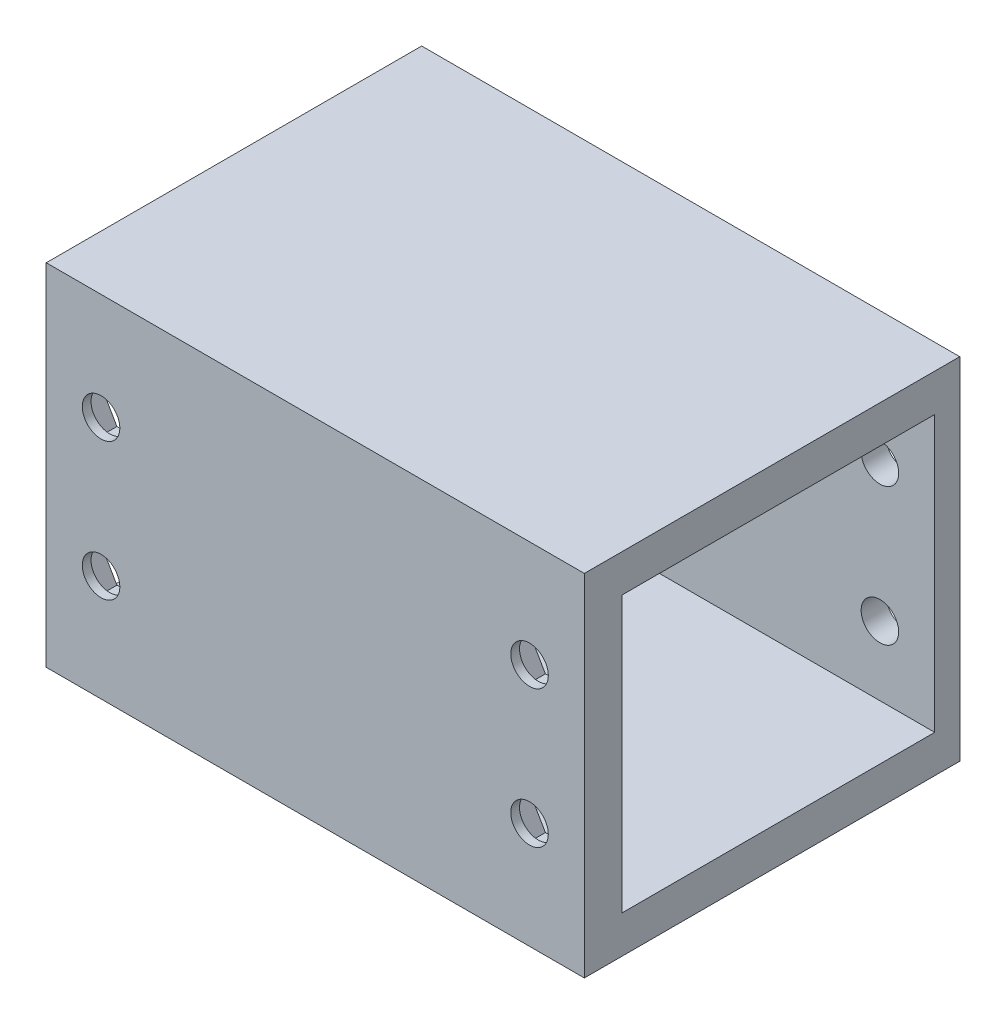
SolidWorks part; units mm, degrees
ref_plane "Front Plane" through (0, 0, 0) normal (0, 0, 1) x (1, 0, 0)
ref_plane "Top Plane" through (0, 0, 0) normal (0, 1, 0) x (1, 0, 0)
ref_plane "Right Plane" through (0, 0, 0) normal (1, 0, 0) x (0, 0, -1)
sketch "Sketch19" plane through (0, 0, 0) normal (1, 0, 0) x (0, 0, -1)
  line L1 (16, 4) -> (-14, 4)
  line L2 (16, 4) -> (16, -24)
  line L3 (16, -24) -> (-14, -24)
  line L4 (-14, 4) -> (-14, -24)
  line L9 (1.5, 1) -> (1.5, -21) construction
  line L10 (-11, -10) -> (14, -10) construction
  line L11 (14, -21) -> (-11, -21)
  line L12 (14, -21) -> (14, 1)
  line L13 (14, 1) -> (-11, 1)
  line L14 (-11, -21) -> (-11, 1)
  line L15 (1.5, 1) -> (1.5, -21) construction
  line L16 (14, -10) -> (-11, -10) construction
  point P4 (1.5, -10)
  point P6 (1.5, -10)
  point P10 (-14, -10)
  dimension "D1" = 30
  dimension "D2" = 3
  dimension "D3" = 3
  dimension "D4" = 2
  dimension "D5" = 3
extrude "Boss-Extrude1" add sketch "Sketch19" against normal blind 43
sketch "Sketch30" plane through (0, 0, 14) normal (0, 0, 1) x (1, 0, 0)
  line L2 (0, -24) -> (0, 4) construction
  line L3 (-43, -24) -> (-43, 4) construction
  circle A0 centre (-38.62, -4.5087) radius 1.5
  circle A1 centre (-4.38, -4.5087) radius 1.5
  circle A2 centre (-4.38, -15.4913) radius 1.5
  circle A3 centre (-38.62, -15.4913) radius 1.5
  point P12 (0, 0)
  point P13 (0, 0)
  point P14 (0, 0)
  point P15 (0, 0)
  dimension "D1" = 3
  dimension "D2" = 3
  dimension "D3" = 3
  dimension "D4" = 3
  dimension "D5" = 4.38
  dimension "D6" = 4.38
  dimension "D7" = 4.38
  dimension "D8" = 4.38
extrude "Cut-Extrude2" cut sketch "Sketch30" against normal through all
sketch "Sketch31" plane through (0, 0, 11) normal (0, 0, -1) x (-1, 0, 0)
  line L1 (42.0841, -4.5087) -> (40.3521, -1.5087)
  line L2 (40.3521, -1.5087) -> (36.8879, -1.5087)
  line L3 (36.8879, -1.5087) -> (35.1559, -4.5087)
  line L4 (35.1559, -4.5087) -> (36.8879, -7.5087)
  line L5 (36.8879, -7.5087) -> (40.3521, -7.5087)
  line L6 (40.3521, -7.5087) -> (42.0841, -4.5087)
  line L7 (7.8441, -4.5087) -> (6.1121, -1.5087)
  line L8 (6.1121, -1.5087) -> (2.6479, -1.5087)
  line L9 (2.6479, -1.5087) -> (0.9159, -4.5087)
  line L10 (0.9159, -4.5087) -> (2.6479, -7.5087)
  line L11 (2.6479, -7.5087) -> (6.1121, -7.5087)
  line L12 (6.1121, -7.5087) -> (7.8441, -4.5087)
  line L13 (7.8441, -15.4913) -> (6.1121, -12.4913)
  line L14 (6.1121, -12.4913) -> (2.6479, -12.4913)
  line L15 (2.6479, -12.4913) -> (0.9159, -15.4913)
  line L16 (0.9159, -15.4913) -> (2.6479, -18.4913)
  line L17 (2.6479, -18.4913) -> (6.1121, -18.4913)
  line L18 (6.1121, -18.4913) -> (7.8441, -15.4913)
  line L19 (42.0841, -15.4913) -> (40.3521, -12.4913)
  line L20 (40.3521, -12.4913) -> (36.8879, -12.4913)
  line L21 (36.8879, -12.4913) -> (35.1559, -15.4913)
  line L22 (35.1559, -15.4913) -> (36.8879, -18.4913)
  line L23 (36.8879, -18.4913) -> (40.3521, -18.4913)
  line L24 (40.3521, -18.4913) -> (42.0841, -15.4913)
  circle A0 centre (38.62, -4.5087) radius 3 construction
  circle A1 centre (4.38, -4.5087) radius 3 construction
  circle A2 centre (4.38, -15.4913) radius 3 construction
  circle A3 centre (38.62, -15.4913) radius 3 construction
  dimension "D1" = 6
extrude "Cut-Extrude4" cut sketch "Sketch31" against normal blind 2.3
